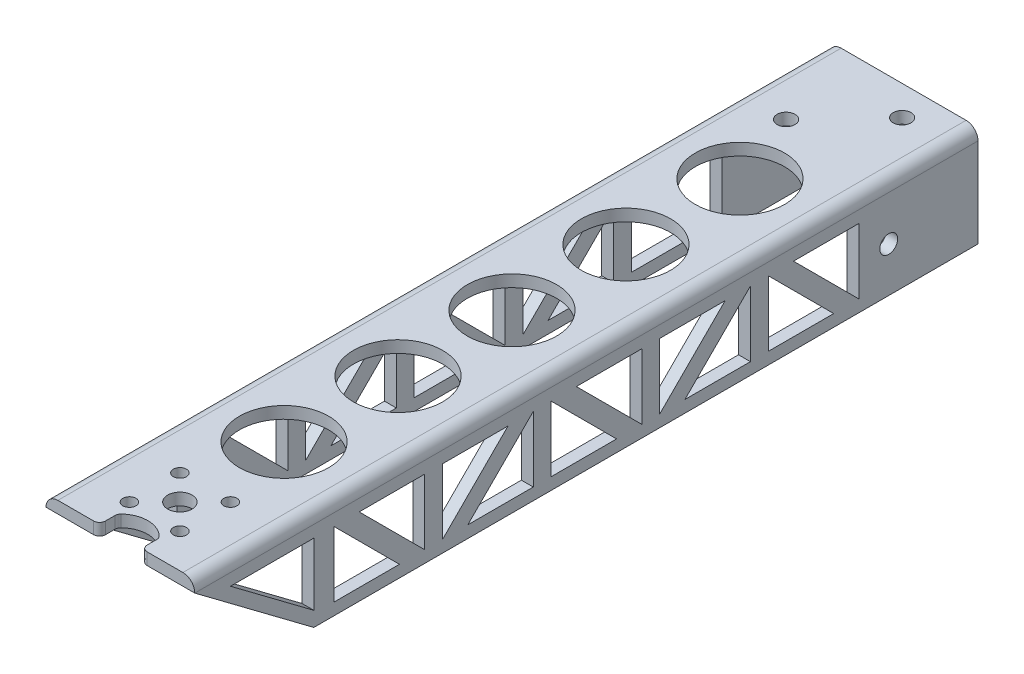
SolidWorks part; units mm, degrees
material "ABS"
ref_plane "Front Plane" through (0, 0, 0) normal (0, 0, 1) x (1, 0, 0)
ref_plane "Top Plane" through (0, 0, 0) normal (0, 1, 0) x (1, 0, 0)
ref_plane "Right Plane" through (0, 0, 0) normal (1, 0, 0) x (0, 0, -1)
sketch "Sketch1" plane through (0, 0, 0) normal (0, 0, 1) x (1, 0, 0)
  line L0 (-12.5, -8.5) -> (-10.5, -8.5)
  line L2 (-12.5, -8.5) -> (-12.5, 6.5)
  line L3 (-10.5, 8.5) -> (10.5, 8.5)
  line L4 (12.5, -8.5) -> (12.5, 6.5)
  line L5 (-12.5, -8.5) -> (12.5, 8.5) construction
  line L6 (-12.5, 8.5) -> (12.5, -8.5) construction
  line L8 (-10.5, -8.5) -> (-10.5, 4.5)
  line L9 (-8.5, 6.5) -> (8.5, 6.5)
  line L10 (10.5, -8.5) -> (10.5, 4.5)
  line L11 (10.5, -8.5) -> (12.5, -8.5)
  arc A0 (10.5, 8.5) -> (12.5, 6.5) centre (10.5, 6.5) cw
  arc A1 (8.5, 6.5) -> (10.5, 4.5) centre (8.5, 4.5) cw
  arc A2 (-12.5, 6.5) -> (-10.5, 8.5) centre (-10.5, 6.5) cw
  arc A3 (-10.5, 4.5) -> (-8.5, 6.5) centre (-8.5, 4.5) cw
  point P0 (0, 0)
  point P11 (0, 6.5)
  point P16 (10.5, 6.5)
  point P22 (-10.5, 6.5)
  dimension "D5" = 2
  dimension "D1" = 21
  dimension "D2" = 2
  dimension "D3" = 2
  dimension "D4" = 17
extrude "Boss-Extrude1" add sketch "Sketch1" along normal blind 20
sketch "Sketch3" plane through (12.5, 0, 0) normal (1, 0, 0) x (0, 0, -1)
  line L0 (0, -8.5) -> (0, 6.5) construction
  line L1 (-20, -8.5) -> (0, -8.5) construction
  circle A0 centre (-15, -1) radius 1.5
  circle A1 centre (-5, -1) radius 1.5
  dimension "D1" = 3
  dimension "D2" = 3
  dimension "D3" = 10
  dimension "D4" = 5
  dimension "D5" = 7.5
extrude "Cut-Extrude1" cut sketch "Sketch3" against normal up to surface (2 mm away) and the other way through all contours A0 up to face at (10.5, -2, 10)
sketch "Sketch17" plane through (-12.5, 0, 0) normal (-1, 0, 0) x (0, 0, 1)
  circle A0 centre (5, -1) radius 1.5
  dimension "D1" = 3
extrude "Cut-Extrude13" cut sketch "Sketch17" against normal up to surface (2 mm away) up to face at (-10.5, -2, 10)
sketch "Sketch4" plane through (0, 8.5, 0) normal (0, 1, 0) x (1, 0, 0)
  line L0 (-10.5, -20) -> (-10.5, 0) construction
  line L1 (-12.5, -20) -> (-12.5, 0) construction
  line L2 (0, 0) -> (0, -20) construction
  line L3 (10.5, -20) -> (-10.5, -20) construction
  line L4 (-10.5, -10) -> (10.5, -10) construction
  line L5 (10.5, -20) -> (10.5, 0) construction
  line L6 (12.5, -20) -> (12.5, 0) construction
  line L7 (10.5, 0) -> (-10.5, 0) construction
  circle A1 centre (-4.75, -15) radius 1.5
  circle A3 centre (4.75, -5) radius 1.5
  dimension "D1" = 7.75
  dimension "D3" = 3
  dimension "D4" = 3
  dimension "D2" = 5
  dimension "D5" = 7.75
  dimension "D6" = 5
extrude "Cut-Extrude2" cut sketch "Sketch4" against normal through all both and the other way through all
sketch "Sketch6" plane through (0, 0, 20) normal (0, 0, 1) x (1, 0, 0)
  line L16 (-12.5, 6.5) -> (-12.5, -8.5)
  line L17 (-12.5, -8.5) -> (-10.5, -8.5)
  line L18 (-10.5, -8.5) -> (-10.5, 4.5)
  line L19 (-8.5, 6.5) -> (8.5, 6.5)
  line L20 (10.5, 4.5) -> (10.5, -8.5)
  line L21 (10.5, -8.5) -> (12.5, -8.5)
  line L22 (12.5, -8.5) -> (12.5, 6.5)
  line L23 (10.5, 8.5) -> (-10.5, 8.5)
  line L24 (-12.5, 6.5) -> (-12.5, -8.5)
  line L25 (-12.5, -8.5) -> (-10.5, -8.5)
  line L26 (-10.5, -8.5) -> (-10.5, 4.5)
  line L27 (-8.5, 6.5) -> (8.5, 6.5)
  line L28 (10.5, 4.5) -> (10.5, -8.5)
  line L29 (10.5, -8.5) -> (12.5, -8.5)
  line L30 (12.5, -8.5) -> (12.5, 6.5)
  line L31 (10.5, 8.5) -> (-10.5, 8.5)
  arc A8 (-8.5, 6.5) -> (-10.5, 4.5) centre (-8.5, 4.5) ccw
  arc A9 (10.5, 4.5) -> (8.5, 6.5) centre (8.5, 4.5) ccw
  arc A10 (12.5, 6.5) -> (10.5, 8.5) centre (10.5, 6.5) ccw
  arc A11 (-10.5, 8.5) -> (-12.5, 6.5) centre (-10.5, 6.5) ccw
  arc A12 (-8.5, 6.5) -> (-10.5, 4.5) centre (-8.5, 4.5) ccw
  arc A13 (10.5, 4.5) -> (8.5, 6.5) centre (8.5, 4.5) ccw
  arc A14 (12.5, 6.5) -> (10.5, 8.5) centre (10.5, 6.5) ccw
  arc A15 (-10.5, 8.5) -> (-12.5, 6.5) centre (-10.5, 6.5) ccw
  dimension "D1" = 0
extrude "Boss-Extrude2" add sketch "Sketch6" along normal blind 111.6
sketch "Sketch7" plane through (0, 8.5, 0) normal (0, 1, 0) x (1, 0, 0)
  line L0 (-10.5, -111.6) -> (10.5, -111.6)
  line L1 (-10.5, -131.6) -> (-10.5, 0) construction
  line L2 (10.5, -131.6) -> (10.5, 0) construction
  line L3 (10.5, -131.6) -> (-10.5, -131.6) construction
  circle A0 centre (0, -104.1) radius 7.5
  dimension "D2" = 15
  dimension "D1" = 20
extrude "Cut-Extrude3" cut sketch "Sketch7" against normal through all contours A0
pattern_linear "LPattern1" count 5 spacing 19.15 along (0, 0, -1) of "Cut-Extrude3"
sketch "Sketch8" plane through (0, 8.5, 0) normal (0, 1, 0) x (1, 0, 0)
  line L0 (10.5, -131.6) -> (-10.5, -131.6) construction
  line L1 (0, -121.6) -> (12.5, -121.6)
  line L2 (12.5, -131.6) -> (12.5, 0) construction
  line L3 (0, -121.6) -> (4.2426, -117.3574)
  line L4 (0, -121.6) -> (0, -115.6)
  circle A0 centre (0, -121.6) radius 6
  circle A1 centre (4.2426, -117.3574) radius 1.1
  circle A2 centre (4.2426, -125.8426) radius 1.1
  circle A3 centre (-4.2426, -125.8426) radius 1.1
  circle A4 centre (-4.2426, -117.3574) radius 1.1
  point P20 (0, -121.6)
  dimension "D1" = 12
  dimension "D3" = 2.2
  dimension "D2" = 10
  dimension "D4" = 45
  dimension "D5" = 4
extrude "Cut-Extrude4" cut sketch "Sketch8" against normal through all contours A0 A3 | A0 A3 | A0 A4 | A0 A4 | A0 A1 L3 | L3 A1 A0 | A0 A1 | A0 A2 | A0 A2
sketch "Sketch9" plane through (12.5, 0, 0) normal (1, 0, 0) x (0, 0, -1)
  line L0 (-131.6, 6.5) -> (-111.6, -8.5)
  line L1 (-131.6, -8.5) -> (0, -8.5) construction
  line L2 (-131.6, -8.5) -> (-131.6, 6.5) construction
  line L3 (-131.6, 6.5) -> (-131.6, -8.5)
  line L4 (-131.6, -8.5) -> (-111.6, -8.5)
  dimension "D1" = 20
extrude "Cut-Extrude6" cut sketch "Sketch9" against normal through all
sketch "Sketch10" plane through (12.5, 0, 0) normal (1, 0, 0) x (0, 0, -1)
  line L0 (-20, -8.5) -> (-20, 6.5)
  line L1 (-111.6, -8.5) -> (0, -8.5) construction
  line L2 (-131.6, 6.5) -> (0, 6.5) construction
  line L3 (0, -8.5) -> (0, 6.5) construction
  line L4 (-111.6, -8.5) -> (-111.6, 6.5)
  line L6 (-20, 4.5) -> (-20, -6.5)
  line L7 (-20, -6.5) -> (-31, 4.5)
  line L8 (-31, 4.5) -> (-20, 4.5)
  dimension "D1" = 20
  dimension "D3" = 2
  dimension "D4" = 2
extrude "Cut-Extrude7" cut sketch "Sketch10" against normal through all contours L8 L7 L6
sketch "Sketch11" plane through (12.5, 0, 0) normal (1, 0, 0) x (0, 0, -1)
  line L0 (-35.2426, 4.5) -> (-24.2426, -6.5)
  line L1 (-24.2426, -6.5) -> (-35.2426, -6.5)
  line L2 (-35.2426, -6.5) -> (-35.2426, 4.5)
  line L3 (-20, -6.5) -> (-31, 4.5) construction
  line L4 (-131.6, 6.5) -> (0, 6.5) construction
  line L5 (-111.6, -8.5) -> (0, -8.5) construction
  dimension "D1" = 3
  dimension "D2" = 2
  dimension "D3" = 2
extrude "Cut-Extrude8" cut sketch "Sketch11" against normal through all
sketch "Sketch12" plane through (12.5, 0, 0) normal (1, 0, 0) x (0, 0, -1)
  line L0 (-38.2426, 4.5) -> (-38.2426, -6.5)
  line L1 (-38.2426, -6.5) -> (-49.2426, -6.5)
  line L2 (-49.2426, -6.5) -> (-38.2426, 4.5)
  line L3 (-35.2426, 4.5) -> (-35.2426, -6.5) construction
  line L4 (-131.6, 6.5) -> (0, 6.5) construction
  line L5 (-111.6, -8.5) -> (0, -8.5) construction
  dimension "D1" = 3
  dimension "D2" = 2
  dimension "D3" = 2
extrude "Cut-Extrude9" cut sketch "Sketch12" against normal through all
sketch "Sketch13" plane through (12.5, 0, 0) normal (1, 0, 0) x (0, 0, -1)
  line L0 (-53.4853, -6.5) -> (-42.4853, 4.5)
  line L1 (-42.4853, 4.5) -> (-53.4853, 4.5)
  line L2 (-53.4853, 4.5) -> (-53.4853, -6.5)
  line L4 (-38.2426, 4.5) -> (-49.2426, -6.5) construction
  line L5 (-131.6, 6.5) -> (0, 6.5) construction
  line L6 (-111.6, -8.5) -> (0, -8.5) construction
  dimension "D1" = 3
  dimension "D2" = 2
  dimension "D3" = 2
extrude "Cut-Extrude10" cut sketch "Sketch13" against normal through all
pattern_linear "LPattern2" count 3 spacing 36.4853 along (0, 0, 1) of "Cut-Extrude7"
pattern_linear "LPattern3" count 3 spacing 36.4853 along (0, 0, 1) of "Cut-Extrude8"
pattern_linear "LPattern4" count 2 spacing 36.4853 along (0, 0, 1) of "Cut-Extrude9"
pattern_linear "LPattern5" count 2 spacing 36.4853 along (0, 0, 1) of "Cut-Extrude10"
sketch "Sketch14" plane through (12.5, 0, 0) normal (1, 0, 0) x (0, 0, -1)
  line L0 (-111.6, -6) -> (-111.6, 4.5)
  line L1 (-111.6, 4.5) -> (-125.6, 4.5)
  line L2 (-125.6, 4.5) -> (-111.6, -6)
  line L4 (-111.6, -8.5) -> (-131.6, 6.5) construction
  line L5 (-131.6, 6.5) -> (0, 6.5) construction
  dimension "D1" = 2
  dimension "D2" = 2
extrude "Cut-Extrude11" cut sketch "Sketch14" against normal through all
sketch "Sketch16" plane through (0, 8.5, 0) normal (0, 1, 0) x (1, 0, 0)
  line L0 (10.5, -131.6) -> (-10.5, -131.6) construction
  circle A0 centre (0, -121.6) radius 6
  circle A1 centre (0, -121.6) radius 2.05
  dimension "D1" = 12
  dimension "D3" = 4.1
  dimension "D2" = 10
extrude "Cut-Extrude12" cut sketch "Sketch16" against normal through all contours A1
sketch "Sketch18" plane through (0, 8.5, 0) normal (0, 1, 0) x (1, 0, 0)
  line L0 (10.5, -131.6) -> (-10.5, -131.6) construction
  line L1 (-3.5, -131.6) -> (3.5, -131.6)
  line L2 (-3.5, -131.6) -> (-3.5, -128.6)
  line L3 (-3.5, -128.6) -> (3.5, -128.6)
  line L4 (3.5, -131.6) -> (3.5, -128.6)
  arc A0 (-3.5, -128.6) -> (3.5, -128.6) centre (0, -131.6) cw
  point P6 (0, -128.6)
  line M19 (-10.5, -131.6) -> (10.5, -131.6)
  dimension "D1" = 3
  dimension "D2" = 7
extrude "Cut-Extrude14" cut sketch "Sketch18" against normal up to surface (2 mm away) contours A0 L3 | L4 L3 L2 M19 up to face at (0, 6.5, 123.65)
fillet "Fillet1" radius 1 4 edges at (3.5, 7.5, 131.6) (-3.5, 7.5, 131.6) (3.5, 7.5, 128.6) (-3.5, 7.5, 128.6)
equation "\"Prop_Length\"= 6in'Diameter Of prop"
equation "\"Prop_Radius\"= \"Prop_Length\" / 2'Radius of Prop"
equation "\"Arm_Distance\"= \"Prop_Radius\" + 1in'Length of arm"
equation "\"Full_Arm_Dist\"= \"Arm_Distance\" + 10mm'Full_Arm_Length"
equation "\"D1@Boss-Extrude2\"=\"Full_Arm_Dist\""
equation "\"Circle_Diameter\"= 15mm'Diameter of the circle on the arm"
equation "\"D2@Sketch7\"=\"Circle_Diameter\""
equation "\"D1@LPattern1\"=int(\"Arm_Distance\"/20)"
